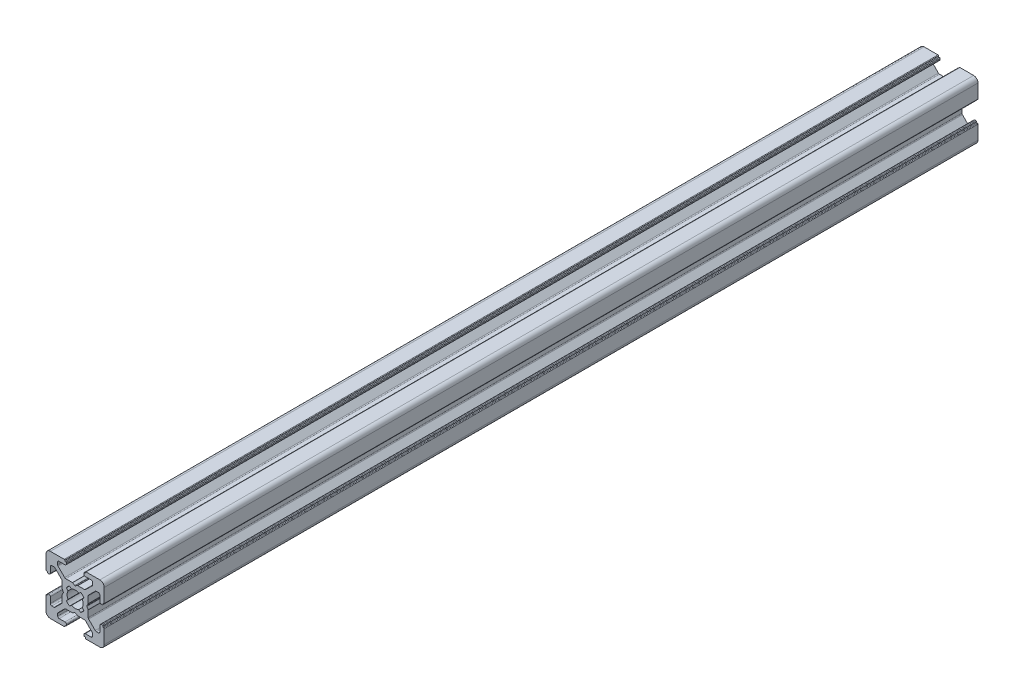
SolidWorks part; units mm, degrees
ref_plane "Płaszczyzna przednia" through (0, 0, 0) normal (0, 0, 1) x (1, 0, 0)
ref_plane "Płaszczyzna górna" through (0, 0, 0) normal (0, 1, 0) x (1, 0, 0)
ref_plane "Płaszczyzna prawa" through (0, 0, 0) normal (1, 0, 0) x (0, 0, -1)
sketch "Szkic1" plane through (0, 0, 0) normal (0, 0, 1) x (1, 0, 0)
  line L0 (7.0078, -1.8401) -> (7.5547, -2.4918)
  line L1 (7.5547, -5.0082) -> (7.0078, -5.6599)
  line L2 (8.0861, -6.7396) -> (8.7418, -6.1953)
  line L3 (11.2582, -6.1953) -> (11.9139, -6.7396)
  line L4 (12.9922, -5.6599) -> (12.4453, -5.0082)
  line L5 (12.4453, -2.4918) -> (12.9922, -1.8401)
  line L6 (11.9139, -0.7604) -> (11.2582, -1.3047)
  line L7 (8.7418, -1.3047) -> (8.0861, -0.7604)
  line L8 (6.25, 6.25) -> (1.5, 6.25)
  line L9 (6.45, 5.95) -> (6.45, 6.05)
  line L10 (6.8, 5.75) -> (6.65, 5.75)
  line L11 (7, 5.25) -> (7, 5.55)
  line L12 (4.5, 4.75) -> (6.5, 4.75)
  line L13 (4, 3.5178) -> (4, 4.25)
  line L14 (6.4142, 0.8964) -> (4.1464, 3.1642)
  line L15 (9.0464, 0.75) -> (6.7678, 0.75)
  line L16 (9.9, 0.2881) -> (9.1464, 0.7232)
  line L17 (10.8536, 0.7232) -> (10.1, 0.2881)
  line L18 (13.2322, 0.75) -> (10.9536, 0.75)
  line L19 (15.8536, 3.1642) -> (13.5858, 0.8964)
  line L20 (16, 4.25) -> (16, 3.5178)
  line L21 (13.5, 4.75) -> (15.5, 4.75)
  line L22 (13, 5.55) -> (13, 5.25)
  line L23 (13.35, 5.75) -> (13.2, 5.75)
  line L24 (13.55, 6.05) -> (13.55, 5.95)
  line L25 (18.5, 6.25) -> (13.75, 6.25)
  line L26 (20, 0) -> (20, 4.75)
  line L27 (19.7, -0.2) -> (19.8, -0.2)
  line L28 (19.5, -0.55) -> (19.5, -0.4)
  line L29 (19, -0.75) -> (19.3, -0.75)
  line L30 (18.5, 1.75) -> (18.5, -0.25)
  line L31 (17.2678, 2.25) -> (18, 2.25)
  line L32 (14.6464, -0.1642) -> (16.9142, 2.1036)
  line L33 (14.5, -2.7964) -> (14.5, -0.5178)
  line L34 (14.0381, -3.65) -> (14.4732, -2.8964)
  line L35 (14.4732, -4.6036) -> (14.0381, -3.85)
  line L36 (14.5, -6.9822) -> (14.5, -4.7036)
  line L37 (16.9142, -9.6036) -> (14.6464, -7.3358)
  line L38 (18, -9.75) -> (17.2678, -9.75)
  line L39 (18.5, -7.25) -> (18.5, -9.25)
  line L40 (19.3, -6.75) -> (19, -6.75)
  line L41 (19.5, -7.1) -> (19.5, -6.95)
  line L42 (19.8, -7.3) -> (19.7, -7.3)
  line L43 (20, -12.25) -> (20, -7.5)
  line L44 (13.75, -13.75) -> (18.5, -13.75)
  line L45 (13.55, -13.45) -> (13.55, -13.55)
  line L46 (13.2, -13.25) -> (13.35, -13.25)
  line L47 (13, -12.75) -> (13, -13.05)
  line L48 (15.5, -12.25) -> (13.5, -12.25)
  line L49 (16, -11.0178) -> (16, -11.75)
  line L50 (13.5858, -8.3964) -> (15.8536, -10.6642)
  line L51 (10.9536, -8.25) -> (13.2322, -8.25)
  line L52 (10.1, -7.7881) -> (10.8536, -8.2232)
  line L53 (9.1464, -8.2232) -> (9.9, -7.7881)
  line L54 (6.7678, -8.25) -> (9.0464, -8.25)
  line L55 (4.1464, -10.6642) -> (6.4142, -8.3964)
  line L56 (4, -11.75) -> (4, -11.0178)
  line L57 (6.5, -12.25) -> (4.5, -12.25)
  line L58 (7, -13.05) -> (7, -12.75)
  line L59 (6.65, -13.25) -> (6.8, -13.25)
  line L60 (6.45, -13.55) -> (6.45, -13.45)
  line L61 (1.5, -13.75) -> (6.25, -13.75)
  line L62 (0, -7.5) -> (0, -12.25)
  line L63 (0.3, -7.3) -> (0.2, -7.3)
  line L64 (0.5, -6.95) -> (0.5, -7.1)
  line L65 (1, -6.75) -> (0.7, -6.75)
  line L66 (1.5, -9.25) -> (1.5, -7.25)
  line L67 (2.7322, -9.75) -> (2, -9.75)
  line L68 (5.3536, -7.3358) -> (3.0858, -9.6036)
  line L69 (5.5, -4.7036) -> (5.5, -6.9822)
  line L70 (5.9619, -3.85) -> (5.5268, -4.6036)
  line L71 (5.5268, -2.8964) -> (5.9619, -3.65)
  line L72 (5.5, -0.5178) -> (5.5, -2.7964)
  line L73 (3.0858, 2.1036) -> (5.3536, -0.1642)
  line L74 (2, 2.25) -> (2.7322, 2.25)
  line L75 (1.5, -0.25) -> (1.5, 1.75)
  line L76 (0.7, -0.75) -> (1, -0.75)
  line L77 (0.5, -0.4) -> (0.5, -0.55)
  line L78 (0.2, -0.2) -> (0.3, -0.2)
  line L79 (0, 4.75) -> (0, 0)
  arc A0 (7.5547, -2.4918) -> (7.5547, -5.0082) centre (10, -3.75) ccw
  arc A1 (7.0078, -5.6599) -> (8.0861, -6.7396) centre (10, -3.75) ccw
  arc A2 (8.7418, -6.1953) -> (11.2582, -6.1953) centre (10, -3.75) ccw
  arc A3 (11.9139, -6.7396) -> (12.9922, -5.6599) centre (10, -3.75) ccw
  arc A4 (12.4453, -5.0082) -> (12.4453, -2.4918) centre (10, -3.75) ccw
  arc A5 (12.9922, -1.8401) -> (11.9139, -0.7604) centre (10, -3.75) ccw
  arc A6 (11.2582, -1.3047) -> (8.7418, -1.3047) centre (10, -3.75) ccw
  arc A7 (8.0861, -0.7604) -> (7.0078, -1.8401) centre (10, -3.75) ccw
  arc A8 (6.45, 6.05) -> (6.25, 6.25) centre (6.25, 6.05) ccw
  arc A9 (6.45, 5.95) -> (6.65, 5.75) centre (6.65, 5.95) ccw
  arc A10 (7, 5.55) -> (6.8, 5.75) centre (6.8, 5.55) ccw
  arc A11 (6.5, 4.75) -> (7, 5.25) centre (6.5, 5.25) ccw
  arc A12 (4.5, 4.75) -> (4, 4.25) centre (4.5, 4.25) ccw
  arc A13 (4, 3.5178) -> (4.1464, 3.1642) centre (4.5, 3.5178) ccw
  arc A14 (6.4142, 0.8964) -> (6.7678, 0.75) centre (6.7678, 1.25) ccw
  arc A15 (9.1464, 0.7232) -> (9.0464, 0.75) centre (9.0464, 0.55) ccw
  arc A16 (9.9, 0.2881) -> (10.1, 0.2881) centre (10, 0.4613) ccw
  arc A17 (10.9536, 0.75) -> (10.8536, 0.7232) centre (10.9536, 0.55) ccw
  arc A18 (13.2322, 0.75) -> (13.5858, 0.8964) centre (13.2322, 1.25) ccw
  arc A19 (15.8536, 3.1642) -> (16, 3.5178) centre (15.5, 3.5178) ccw
  arc A20 (16, 4.25) -> (15.5, 4.75) centre (15.5, 4.25) ccw
  arc A21 (13, 5.25) -> (13.5, 4.75) centre (13.5, 5.25) ccw
  arc A22 (13.2, 5.75) -> (13, 5.55) centre (13.2, 5.55) ccw
  arc A23 (13.35, 5.75) -> (13.55, 5.95) centre (13.35, 5.95) ccw
  arc A24 (13.75, 6.25) -> (13.55, 6.05) centre (13.75, 6.05) ccw
  arc A25 (20, 4.75) -> (18.5, 6.25) centre (18.5, 4.75) ccw
  arc A26 (19.8, -0.2) -> (20, 0) centre (19.8, 0) ccw
  arc A27 (19.7, -0.2) -> (19.5, -0.4) centre (19.7, -0.4) ccw
  arc A28 (19.3, -0.75) -> (19.5, -0.55) centre (19.3, -0.55) ccw
  arc A29 (18.5, -0.25) -> (19, -0.75) centre (19, -0.25) ccw
  arc A30 (18.5, 1.75) -> (18, 2.25) centre (18, 1.75) ccw
  arc A31 (17.2678, 2.25) -> (16.9142, 2.1036) centre (17.2678, 1.75) ccw
  arc A32 (14.6464, -0.1642) -> (14.5, -0.5178) centre (15, -0.5178) ccw
  arc A33 (14.4732, -2.8964) -> (14.5, -2.7964) centre (14.3, -2.7964) ccw
  arc A34 (14.0381, -3.65) -> (14.0381, -3.85) centre (14.2113, -3.75) ccw
  arc A35 (14.5, -4.7036) -> (14.4732, -4.6036) centre (14.3, -4.7036) ccw
  arc A36 (14.5, -6.9822) -> (14.6464, -7.3358) centre (15, -6.9822) ccw
  arc A37 (16.9142, -9.6036) -> (17.2678, -9.75) centre (17.2678, -9.25) ccw
  arc A38 (18, -9.75) -> (18.5, -9.25) centre (18, -9.25) ccw
  arc A39 (19, -6.75) -> (18.5, -7.25) centre (19, -7.25) ccw
  arc A40 (19.5, -6.95) -> (19.3, -6.75) centre (19.3, -6.95) ccw
  arc A41 (19.5, -7.1) -> (19.7, -7.3) centre (19.7, -7.1) ccw
  arc A42 (20, -7.5) -> (19.8, -7.3) centre (19.8, -7.5) ccw
  arc A43 (18.5, -13.75) -> (20, -12.25) centre (18.5, -12.25) ccw
  arc A44 (13.55, -13.55) -> (13.75, -13.75) centre (13.75, -13.55) ccw
  arc A45 (13.55, -13.45) -> (13.35, -13.25) centre (13.35, -13.45) ccw
  arc A46 (13, -13.05) -> (13.2, -13.25) centre (13.2, -13.05) ccw
  arc A47 (13.5, -12.25) -> (13, -12.75) centre (13.5, -12.75) ccw
  arc A48 (15.5, -12.25) -> (16, -11.75) centre (15.5, -11.75) ccw
  arc A49 (16, -11.0178) -> (15.8536, -10.6642) centre (15.5, -11.0178) ccw
  arc A50 (13.5858, -8.3964) -> (13.2322, -8.25) centre (13.2322, -8.75) ccw
  arc A51 (10.8536, -8.2232) -> (10.9536, -8.25) centre (10.9536, -8.05) ccw
  arc A52 (10.1, -7.7881) -> (9.9, -7.7881) centre (10, -7.9613) ccw
  arc A53 (9.0464, -8.25) -> (9.1464, -8.2232) centre (9.0464, -8.05) ccw
  arc A54 (6.7678, -8.25) -> (6.4142, -8.3964) centre (6.7678, -8.75) ccw
  arc A55 (4.1464, -10.6642) -> (4, -11.0178) centre (4.5, -11.0178) ccw
  arc A56 (4, -11.75) -> (4.5, -12.25) centre (4.5, -11.75) ccw
  arc A57 (7, -12.75) -> (6.5, -12.25) centre (6.5, -12.75) ccw
  arc A58 (6.8, -13.25) -> (7, -13.05) centre (6.8, -13.05) ccw
  arc A59 (6.65, -13.25) -> (6.45, -13.45) centre (6.65, -13.45) ccw
  arc A60 (6.25, -13.75) -> (6.45, -13.55) centre (6.25, -13.55) ccw
  arc A61 (0, -12.25) -> (1.5, -13.75) centre (1.5, -12.25) ccw
  arc A62 (0.2, -7.3) -> (0, -7.5) centre (0.2, -7.5) ccw
  arc A63 (0.3, -7.3) -> (0.5, -7.1) centre (0.3, -7.1) ccw
  arc A64 (0.7, -6.75) -> (0.5, -6.95) centre (0.7, -6.95) ccw
  arc A65 (1.5, -7.25) -> (1, -6.75) centre (1, -7.25) ccw
  arc A66 (1.5, -9.25) -> (2, -9.75) centre (2, -9.25) ccw
  arc A67 (2.7322, -9.75) -> (3.0858, -9.6036) centre (2.7322, -9.25) ccw
  arc A68 (5.3536, -7.3358) -> (5.5, -6.9822) centre (5, -6.9822) ccw
  arc A69 (5.5268, -4.6036) -> (5.5, -4.7036) centre (5.7, -4.7036) ccw
  arc A70 (5.9619, -3.85) -> (5.9619, -3.65) centre (5.7887, -3.75) ccw
  arc A71 (5.5, -2.7964) -> (5.5268, -2.8964) centre (5.7, -2.7964) ccw
  arc A72 (5.5, -0.5178) -> (5.3536, -0.1642) centre (5, -0.5178) ccw
  arc A73 (3.0858, 2.1036) -> (2.7322, 2.25) centre (2.7322, 1.75) ccw
  arc A74 (2, 2.25) -> (1.5, 1.75) centre (2, 1.75) ccw
  arc A75 (1, -0.75) -> (1.5, -0.25) centre (1, -0.25) ccw
  arc A76 (0.5, -0.55) -> (0.7, -0.75) centre (0.7, -0.55) ccw
  arc A77 (0.5, -0.4) -> (0.3, -0.2) centre (0.3, -0.4) ccw
  arc A78 (0, 0) -> (0.2, -0.2) centre (0.2, 0) ccw
  arc A79 (1.5, 6.25) -> (0, 4.75) centre (1.5, 4.75) ccw
  dimension "D4" = 2.75
  dimension "D1" = 20
  dimension "D2" = 20
  dimension "D3" = 6
extrude "Dodanie-wyciągnięcie1" add sketch "Szkic1" along normal blind 300
